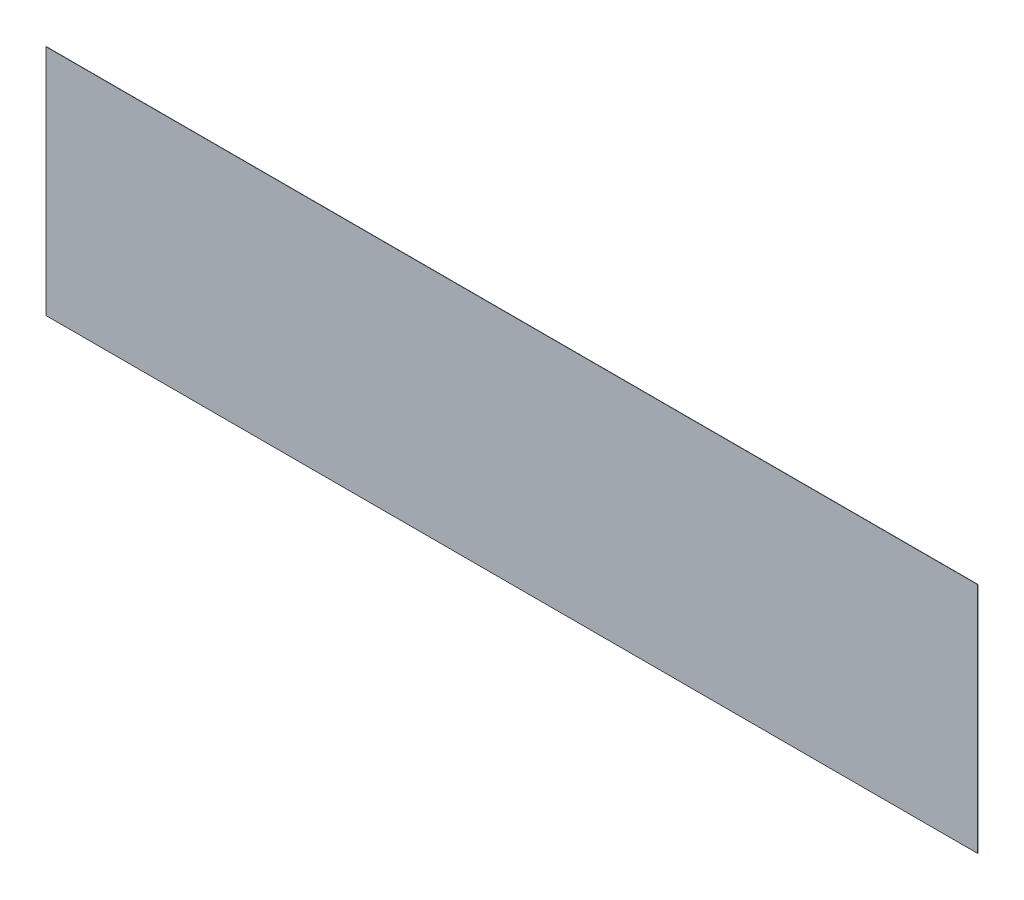
SolidWorks part; units mm, degrees
ref_plane "Front Plane" through (0, 0, 0) normal (0, 0, 1) x (1, 0, 0)
ref_plane "Top Plane" through (0, 0, 0) normal (0, 1, 0) x (1, 0, 0)
ref_plane "Right Plane" through (0, 0, 0) normal (1, 0, 0) x (0, 0, -1)
sketch "Sketch1" plane through (0, 0, 0) normal (0, 0, 1) x (1, 0, 0)
  line L1 (344.551, 86.106) -> (-344.551, 86.106)
  line L2 (344.551, 86.106) -> (344.551, -86.106)
  line L3 (344.551, -86.106) -> (-344.551, -86.106)
  line L4 (-344.551, 86.106) -> (-344.551, -86.106)
  line L5 (344.551, 86.106) -> (-344.551, -86.106) construction
  line L6 (344.551, -86.106) -> (-344.551, 86.106) construction
  point P0 (0, 0)
  dimension "D1" = 172.212
  dimension "D2" = 689.102
extrude "Boss-Extrude1" add sketch "Sketch1" along normal mid plane 0.2032
